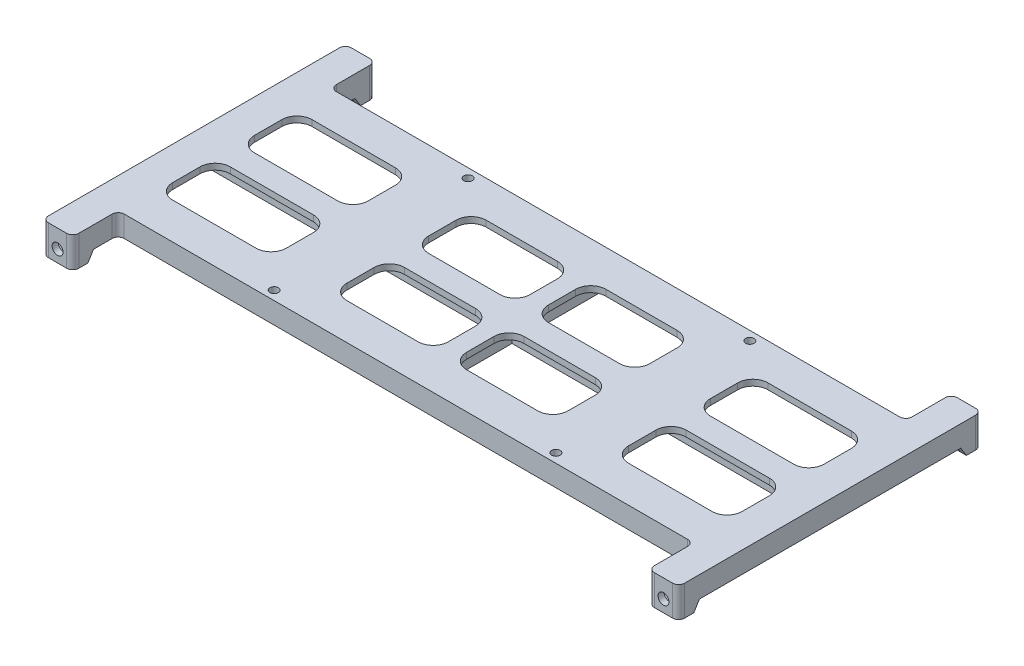
SolidWorks part; units mm, degrees
material "ABS"
ref_plane "前视基准面" through (0, 0, 0) normal (0, 0, 1) x (1, 0, 0)
ref_plane "上视基准面" through (0, 0, 0) normal (0, 1, 0) x (1, 0, 0)
ref_plane "右视基准面" through (0, 0, 0) normal (1, 0, 0) x (0, 0, -1)
sketch "草图1" plane through (0, 0, 0) normal (0, 1, 0) x (1, 0, 0)
  line L1 (-105, 50) -> (105, 50)
  line L2 (-105, 50) -> (-105, -50)
  line L3 (-105, -50) -> (105, -50)
  line L4 (105, 50) -> (105, -50)
  line L5 (-105, 50) -> (105, -50) construction
  line L6 (-105, -50) -> (105, 50) construction
  point P0 (0, 0)
  dimension "D1" = 100
  dimension "D2" = 210
extrude "凸台-拉伸1" add sketch "草图1" along normal blind 2
sketch "草图3" plane through (0, 0, 50) normal (0, 0, 1) x (1, 0, 0)
  line L0 (-105, 0) -> (105, 0) construction
  line L1 (-105, 0) -> (-95, 0)
  line L2 (-105, 0) -> (-105, -8)
  line L3 (-105, -8) -> (-95, -8)
  line L4 (-95, 0) -> (-95, -8)
  dimension "D1" = 10
  dimension "D2" = 8
extrude "凸台-拉伸2" add sketch "草图3" against normal blind 5
sketch "草图4" plane through (0, 0, 50) normal (0, 0, 1) x (1, 0, 0)
  line L0 (-105, -8) -> (-95, -8) construction
  circle A0 centre (-100, -4) radius 1.8
  point P4 (-90.8057, -3)
  point P5 (-100, -8)
  point P6 (-100, -3)
  dimension "D1" = 4
  dimension "D2" = 3.6
extrude "切除-拉伸1" cut sketch "草图4" against normal blind 5 contours A0
sketch "草图5" plane through (-105, 0, 0) normal (-1, 0, 0) x (0, 0, 1)
  line L0 (40, 0) -> (45, -8)
  line L1 (-50, 0) -> (45, 0) construction
  dimension "D1" = 5
rib "筋3" sketch "草图5" sketch "草图5" thickness 2 extrusion direction parallel to sketch draft on no parameters "D1"=2
ref_plane "基准面1" through (-100, 0, 0) normal (-1, 0, 0) x (0, 0, 1)
mirror "镜向1" about plane through (-100, 0, 0) normal (-1, 0, 0) of "筋3"
sketch "草图6" plane through (0, 0, 45) normal (0, 0, -1) x (-1, 0, 0)
  line L0 (100, -5.5) -> (100, 5.5) construction
  line L1 (100, -7.2332) -> (102.8, -5.6166)
  line L2 (102.8, -5.6166) -> (102.8, -2.3834)
  line L3 (102.8, -2.3834) -> (100, -0.7668)
  line L4 (100, -0.7668) -> (97.2, -2.3834)
  line L5 (97.2, -2.3834) -> (97.2, -5.6166)
  line L6 (97.2, -5.6166) -> (100, -7.2332)
  circle A0 centre (100, -4) radius 2.8 construction
  point P10 (100, -3.5)
  point P12 (102.064, -5.5572)
  point P13 (0, 0)
  point P14 (102.6306, -1.9812)
  dimension "D1" = 5.6
extrude "切除-拉伸2" cut sketch "草图6" against normal blind 3
mirror "镜向2" about plane through (0, 0, 0) normal (0, 0, 1) of "切除-拉伸2", "镜向1", "筋3", "切除-拉伸1", "凸台-拉伸2" second plane through (0, 0, 0) second plane normal (1, 0, 0)
sketch "草图19" plane through (0, 0, 0) normal (0, -1, 0) x (1, 0, 0)
  line L0 (95, 40) -> (95, 50) construction
  line L1 (-95, 50) -> (95, 50)
  line L2 (-95, 50) -> (-95, 35)
  line L3 (-95, 35) -> (95, 35)
  line L4 (95, 50) -> (95, 35)
  line L5 (5.5, 0) -> (-5.5, 0) construction
  line L6 (-95, -35) -> (95, -35)
  line L7 (95, -50) -> (95, -35)
  line L8 (-95, -50) -> (95, -50)
  line L9 (-95, -50) -> (-95, -35)
  dimension "D1" = 70
extrude "切除-拉伸5" cut sketch "草图19" against normal through all
sketch "草图7" plane through (0, 0, 0) normal (0, -1, 0) x (1, 0, 0)
  line L16 (-95, 40) -> (-95, 45) construction
  line L17 (-97, 45) -> (-95, 45) construction
  line L18 (-97, 40) -> (-97, 45) construction
  line L19 (97, 33) -> (97, 40)
  line L20 (-97, 33) -> (97, 33)
  line L21 (-97, 40) -> (-97, 33)
  line L22 (97, 33) -> (97, 40)
  line L23 (-97, 33) -> (97, 33)
  line L24 (-97, 40) -> (-97, 33)
  line L25 (97, 40) -> (97, 45) construction
  line L26 (95, 40) -> (95, 45) construction
  line L27 (97, 45) -> (95, 45) construction
  line L28 (95, 35) -> (95, 40) construction
  line L29 (-95, 35) -> (95, 35) construction
  line L30 (-95, 40) -> (-95, 35) construction
  line L31 (-95, 40) -> (-95, 45)
  line L32 (-97, 45) -> (-95, 45)
  line L33 (-97, 40) -> (-97, 45)
  line L34 (97, 40) -> (97, 45)
  line L35 (95, 40) -> (95, 45)
  line L36 (97, 45) -> (95, 45)
  line L37 (95, 35) -> (95, 40)
  line L38 (-95, 35) -> (95, 35)
  line L39 (-95, 40) -> (-95, 35)
  line L40 (5.5, 0) -> (-5.5, 0) construction
  line L41 (-95, -40) -> (-95, -35)
  line L42 (-95, -35) -> (95, -35)
  line L43 (95, -35) -> (95, -40)
  line L44 (97, -45) -> (95, -45)
  line L45 (95, -40) -> (95, -45)
  line L46 (97, -40) -> (97, -45)
  line L47 (-97, -40) -> (-97, -45)
  line L48 (-97, -45) -> (-95, -45)
  line L49 (-95, -40) -> (-95, -45)
  line L50 (-97, -40) -> (-97, -33)
  line L51 (-97, -33) -> (97, -33)
  line L52 (97, -33) -> (97, -40)
  dimension "D1" = 2
extrude "凸台-拉伸3" add sketch "草图7" along normal blind 5
sketch "草图10" plane through (0, 0, 0) normal (0, -1, 0) x (1, 0, 0)
  line L0 (-105, -40) -> (-105, 40) construction
  line L1 (-105, 45) -> (-103, 45)
  line L2 (-105, 45) -> (-105, -45)
  line L3 (-105, -45) -> (-103, -45)
  line L4 (-103, 45) -> (-103, -45)
  line L5 (-103, 40) -> (-103, 45) construction
  line L6 (-103, 45) -> (-97, 45) construction
  point P6 (-105, 0)
  point P7 (-105, 0)
extrude "凸台-拉伸4" add sketch "草图10" along normal up to surface (5 mm away) up to face at (0, -5, 38.5625)
mirror "镜向3" about plane through (0, 0, 0) normal (1, 0, 0) of "凸台-拉伸4"
sketch "草图11" plane through (0, 0, 0) normal (0, -1, 0) x (1, 0, 0)
  line L1 (-1, 35) -> (1, 35)
  line L2 (-1, 35) -> (-1, -35)
  line L3 (-1, -35) -> (1, -35)
  line L4 (1, 35) -> (1, -35)
  line L5 (95, -35) -> (-95, -35) construction
  line L6 (95, 35) -> (-95, 35) construction
  point P4 (1, 35)
  point P8 (0, 35)
  dimension "D1" = 2
extrude "凸台-拉伸5" add sketch "草图11" along normal up to surface (5 mm away) up to face at (-104, -5, 0)
sketch "草图12" plane through (0, 0, 0) normal (0, -1, 0) x (1, 0, 0)
  line L0 (-103, -43.125) -> (-103, 43.125) construction
  line L1 (-103, 1) -> (103, 1)
  line L2 (-103, 1) -> (-103, -1)
  line L3 (-103, -1) -> (103, -1)
  line L4 (103, 1) -> (103, -1)
  line L5 (103, -43.125) -> (103, 43.125) construction
  point P4 (103, 0)
  dimension "D1" = 2
extrude "凸台-拉伸6" add sketch "草图12" along normal up to surface (5 mm away) up to face at (-104, -5, 0)
sketch "草图13" plane through (0, 0, 0) normal (0, -1, 0) x (1, 0, 0)
  line L1 (-46.5, 32) -> (46.5, 32) construction
  line L2 (-46.5, 32) -> (-46.5, -32) construction
  line L3 (-46.5, -32) -> (46.5, -32) construction
  line L4 (46.5, 32) -> (46.5, -32) construction
  line L5 (-46.5, 32) -> (46.5, -32) construction
  line L6 (-46.5, -32) -> (46.5, 32) construction
  circle A0 centre (-46.5, 32) radius 3
  circle A1 centre (46.5, 32) radius 3 construction
  circle A2 centre (46.5, -32) radius 3 construction
  circle A3 centre (-46.5, -32) radius 3 construction
  point P0 (0, 0)
  dimension "D3" = 6
  dimension "D1" = 93
  dimension "D2" = 64
extrude "凸台-拉伸7" add sketch "草图13" along normal up to surface (5 mm away) up to face at (0, -5, 0)
sketch "草图15" plane through (0, -5, 0) normal (0, -1, 0) x (1, 0, 0)
  circle A0 centre (-46.5, 32) radius 1.4
  point P3 (-46.5, 32)
  dimension "D1" = 2.8
extrude "切除-拉伸3" cut sketch "草图15" against normal through all
mirror "镜向4" about plane through (0, 0, 0) normal (1, 0, 0) of "切除-拉伸3", "凸台-拉伸7" second plane through (0, 0, 0) second plane normal (0, 0, 1)
fillet "圆角1" radius 2 4 edges at (105, -3, 50) (-105, -3, 50) (105, -3, -50) (-105, -3, -50)
sketch "草图17" plane through (0, 0, 0) normal (0, -1, 0) x (1, 0, 0)
  line L1 (-94, 23) -> (-56.5, 23)
  line L2 (-94, 23) -> (-94, 4)
  line L3 (-94, 4) -> (-56.5, 4)
  line L4 (-56.5, 23) -> (-56.5, 4)
  line L5 (-103, 1) -> (-103, 45) construction
  line L7 (-1, 1) -> (-103, 1) construction
  line L8 (0, -5.5) -> (0, 5.5) construction
  line L9 (56.5, 23) -> (56.5, 4)
  line L10 (94, 4) -> (56.5, 4)
  line L11 (94, 23) -> (94, 4)
  line L12 (94, 23) -> (56.5, 23)
  line L13 (5.5, 0) -> (-5.5, 0) construction
  line L14 (94, -23) -> (56.5, -23)
  line L15 (94, -23) -> (94, -4)
  line L16 (94, -4) -> (56.5, -4)
  line L17 (56.5, -23) -> (56.5, -4)
  line L18 (-56.5, -23) -> (-56.5, -4)
  line L19 (-94, -4) -> (-56.5, -4)
  line L20 (-94, -23) -> (-94, -4)
  line L21 (-94, -23) -> (-56.5, -23)
  line L22 (-36.5, 23) -> (-3, 23)
  line L23 (-36.5, 23) -> (-36.5, 4)
  line L24 (-36.5, 4) -> (-3, 4)
  line L25 (-3, 23) -> (-3, 4)
  line L27 (-1, 33) -> (-1, 1) construction
  line L28 (36.5, 23) -> (36.5, 4)
  line L29 (36.5, 4) -> (3, 4)
  line L30 (3, 23) -> (3, 4)
  line L31 (36.5, 23) -> (3, 23)
  line L32 (36.5, -23) -> (3, -23)
  line L33 (3, -23) -> (3, -4)
  line L34 (36.5, -4) -> (3, -4)
  line L35 (36.5, -23) -> (36.5, -4)
  line L36 (-36.5, -23) -> (-36.5, -4)
  line L37 (-36.5, -4) -> (-3, -4)
  line L38 (-3, -23) -> (-3, -4)
  line L39 (-36.5, -23) -> (-3, -23)
  line L40 (-97, 33) -> (-49.3284, 33) construction
  line L41 (-56.5, 23) -> (-36.5, 23) construction
  point P8 (-46.5, 23)
  point P9 (-46.5, 32)
  dimension "D1" = 10
  dimension "D2" = 9
  dimension "D3" = 20
  dimension "D4" = 3
  dimension "D6" = 2
extrude "切除-拉伸4" cut sketch "草图17" against normal through all
fillet "圆角2" radius 5 32 edges at (-56.5, 1, 4) (-94, 1, 4) (94, 1, 23) (94, 1, 4) (56.5, 1, 4) (56.5, 1, 23) (94, 1, -23) (56.5, 1, -23) (56.5, 1, -4) (94, 1, -4) (-94, 1, -23) (-94, 1, -4) (-56.5, 1, -4) (-56.5, 1, -23) (-56.5, 1, 23) (-94, 1, 23) (-36.5, 1, -4) (-3, 1, -4) (-3, 1, -23) (36.5, 1, -23) (3, 1, -23) (3, 1, -4) (36.5, 1, -4) (36.5, 1, 23) (36.5, 1, 4) (3, 1, 4) (3, 1, 23) (-36.5, 1, 23) (-3, 1, 23) (-3, 1, 4) (-36.5, 1, 4) (-36.5, 1, -23)
fillet "圆角3" radius 2 8 edges at (95, -3, 50) (-95, -3, -50) (95, -3, -50) (-95, -3, 50) (-95, -1.5, 35) (95, -1.5, 35) (-95, -1.5, -35) (95, -1.5, -35)
fillet "圆角4" radius 4 4 edges at (-97, -2.5, 33) (-97, -2.5, -33) (97, -2.5, 33) (97, -2.5, -33)
